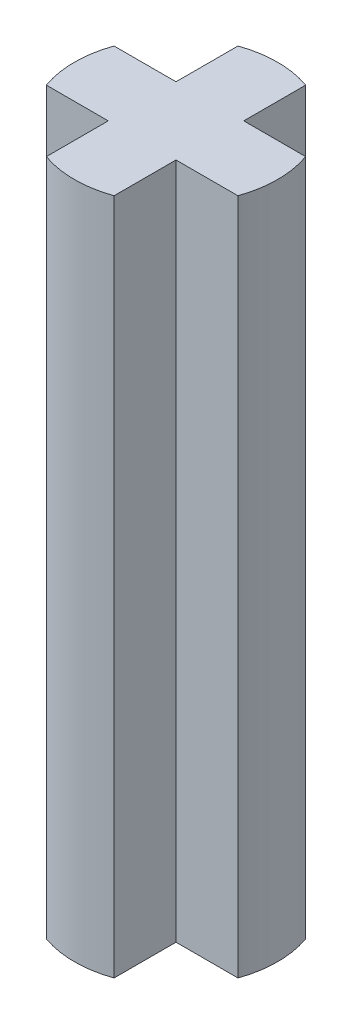
SolidWorks part; units mm, degrees
ref_plane "Front Plane" through (0, 0, 0) normal (0, 0, 1) x (1, 0, 0)
ref_plane "Top Plane" through (0, 0, 0) normal (0, 1, 0) x (1, 0, 0)
ref_plane "Right Plane" through (0, 0, 0) normal (1, 0, 0) x (0, 0, -1)
sketch "Sketch1" plane through (0, 0, 0) normal (0, 1, 0) x (1, 0, 0)
  line L1 (-1.5, -0.5) -> (1.5, -0.5)
  line L2 (-1.5, -0.5) -> (-1.5, 0.5)
  line L3 (-1.5, 0.5) -> (1.5, 0.5)
  line L4 (1.5, -0.5) -> (1.5, 0.5)
  line L5 (-1.5, -0.5) -> (1.5, 0.5) construction
  line L6 (-1.5, 0.5) -> (1.5, -0.5) construction
  line L7 (-0.5, -1.5) -> (0.5, -1.5)
  line L8 (-0.5, -1.5) -> (-0.5, 1.5)
  line L9 (-0.5, 1.5) -> (0.5, 1.5)
  line L10 (0.5, -1.5) -> (0.5, 1.5)
  line L11 (-0.5, -1.5) -> (0.5, 1.5) construction
  line L12 (-0.5, 1.5) -> (0.5, -1.5) construction
  point P0 (0, 0)
  point P6 (0, 0)
  dimension "D1" = 1
  dimension "D2" = 3
extrude "Boss-Extrude1" add sketch "Sketch1" along normal blind 10 contours L4 L3 L2 L1 | L10 L9 L8 L7
sketch "Sketch2" plane through (0, 10, 0) normal (0, 1, 0) x (1, 0, 0)
  circle A0 centre (0, 0) radius 1.5
extrude "Cut-Extrude1" cut sketch "Sketch2" against normal up to next (10 mm away) flip side to cut
